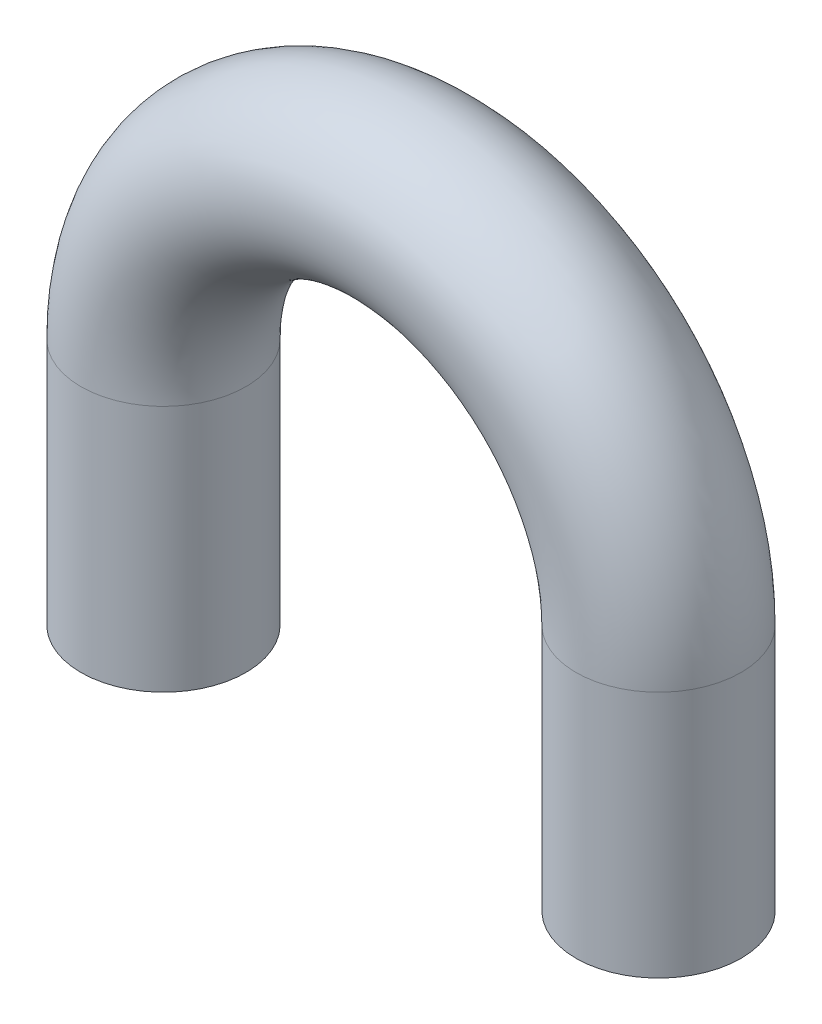
SolidWorks part; units mm, degrees
material "Bronze d'aluminium"
ref_plane "Face" through (0, 0, 0) normal (0, 0, 1) x (1, 0, 0)
ref_plane "Dessus" through (0, 0, 0) normal (0, 1, 0) x (1, 0, 0)
ref_plane "Droite" through (0, 0, 0) normal (1, 0, 0) x (0, 0, -1)
sketch "Esquisse1" plane through (0, 0, 0) normal (0, 0, 1) x (1, 0, 0)
  line L0 (-3, 3) -> (-3, 0)
  line L1 (3, 3) -> (3, 0)
  arc A0 (3, 3) -> (-3, 3) centre (0, 3) ccw
  dimension "D1" = 3
  dimension "D2" = 3
sketch "Esquisse3" plane through (0, 0, 0) normal (0, 1, 0) x (1, 0, 0)
  circle A0 centre (3, 0) radius 1
  dimension "D1" = 2
sweep "Balayage1" add profiles "Esquisse3" path "Esquisse1"
